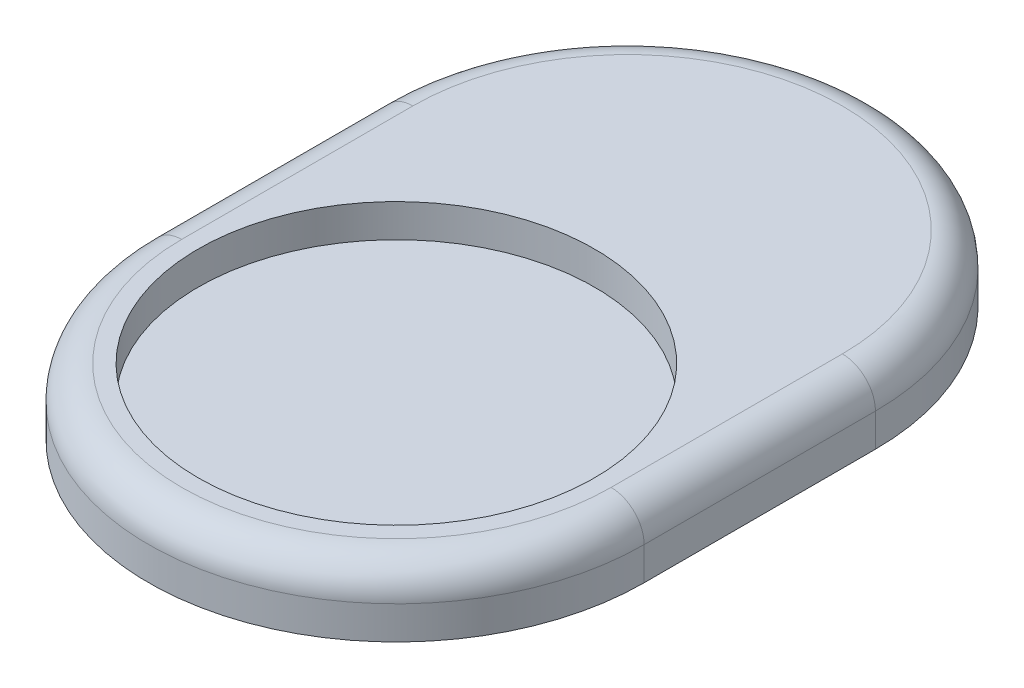
SolidWorks part; units mm, degrees
ref_plane "Front Plane" through (0, 0, 0) normal (0, 0, 1) x (1, 0, 0)
ref_plane "Top Plane" through (0, 0, 0) normal (0, 1, 0) x (1, 0, 0)
ref_plane "Right Plane" through (0, 0, 0) normal (1, 0, 0) x (0, 0, -1)
sketch "Sketch2" plane through (0, 0, 0) normal (0, 1, 0) x (1, 0, 0)
  line L0 (0, 0) -> (0, 7) construction
  line L1 (-7.5, 0) -> (-7.5, 7)
  line L2 (7.5, 0) -> (7.5, 7)
  arc A0 (-7.5, 0) -> (7.5, 0) centre (0, 0) ccw
  arc A1 (7.5, 7) -> (-7.5, 7) centre (0, 7) ccw
  point P3 (0, 3.5)
extrude "Boss-Extrude2" add sketch "Sketch2" along normal blind 2 contours L2 A1 L1 A0
sketch "Sketch3" plane through (0, 2, 0) normal (0, 1, 0) x (1, 0, 0)
  circle A0 centre (0, 0) radius 6
extrude "Cut-Extrude1" cut sketch "Sketch3" against normal blind 1
fillet "Fillet2" radius 1 4 edges at (0, 2, 7.5) (7.5, 2, -3.5) (0, 2, -14.5) (-7.5, 2, -3.5)
